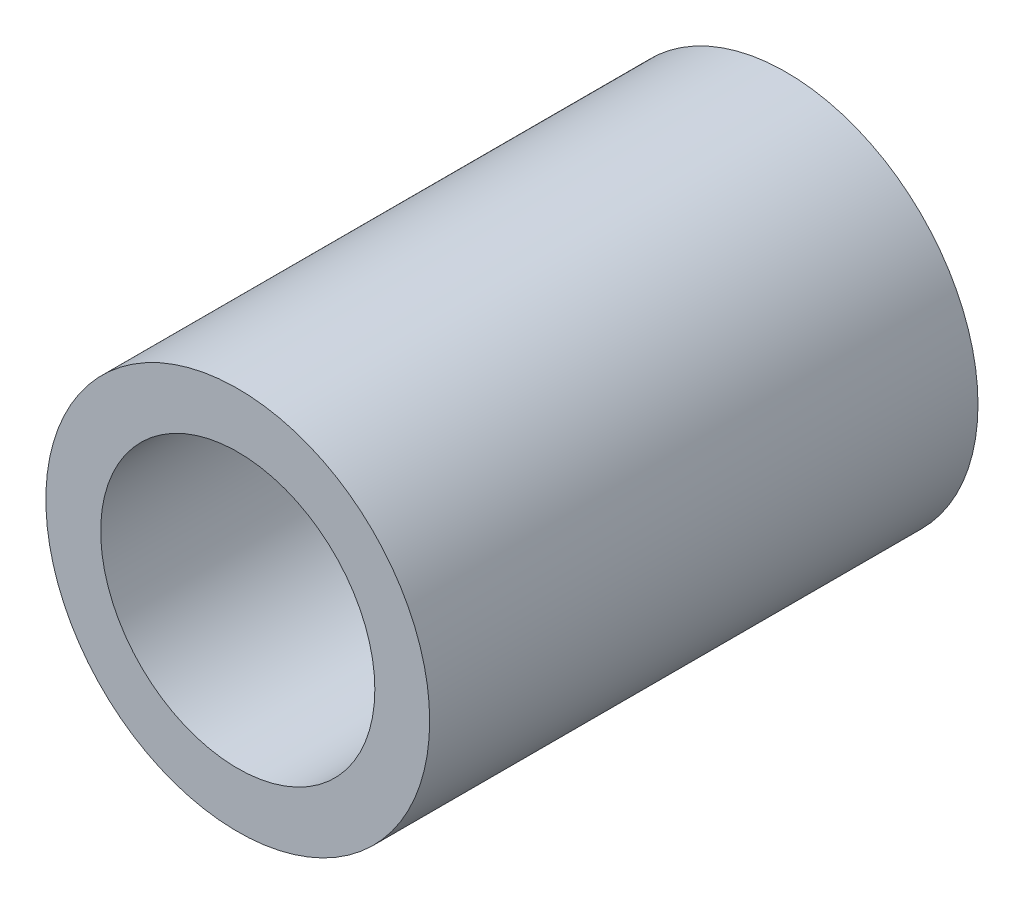
SolidWorks part; units mm, degrees
material "Brass"
ref_plane "Front Plane" through (0, 0, 0) normal (0, 0, 1) x (1, 0, 0)
ref_plane "Top Plane" through (0, 0, 0) normal (0, 1, 0) x (1, 0, 0)
ref_plane "Right Plane" through (0, 0, 0) normal (1, 0, 0) x (0, 0, -1)
sketch "Sketch1" plane through (0, 0, 0) normal (0, 0, 1) x (1, 0, 0)
  circle A0 centre (0, 0) radius 2.5
  circle A1 centre (0, 0) radius 3.5
extrude "Boss-Extrude1" add sketch "Sketch1" along normal blind 10
